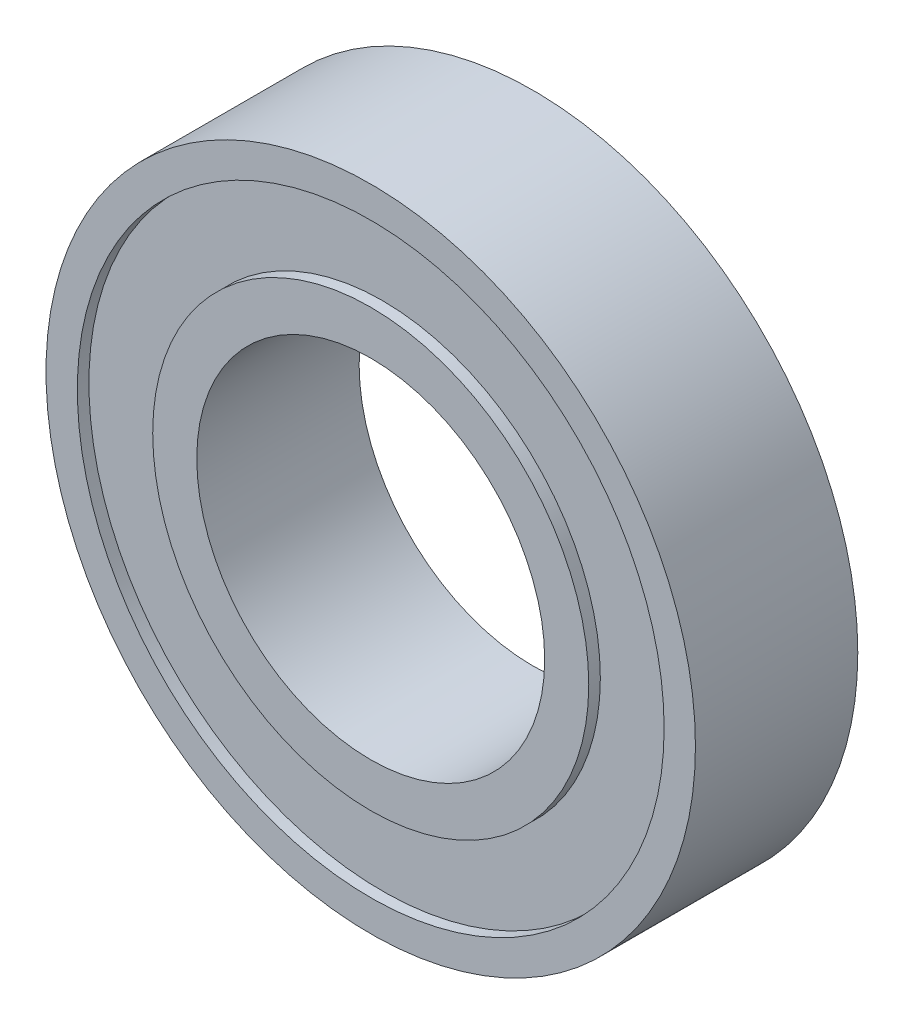
SolidWorks part; units mm, degrees
ref_plane "前基準面" through (0, 0, 0) normal (0, 0, 1) x (1, 0, 0)
ref_plane "上基準面" through (0, 0, 0) normal (0, 1, 0) x (1, 0, 0)
ref_plane "右基準面" through (0, 0, 0) normal (1, 0, 0) x (0, 0, -1)
sketch "草圖1" plane through (0, 0, 0) normal (0, 0, 1) x (1, 0, 0)
  circle A0 centre (0, 0) radius 14
  dimension "D1" = 28
extrude "填料-伸長1" add sketch "草圖1" along normal blind 7
sketch "草圖2" plane through (0, 0, 7) normal (0, 0, 1) x (1, 0, 0)
  circle A0 centre (0, 0) radius 7.5
  dimension "D1" = 15
extrude "除料-伸長1" cut sketch "草圖2" against normal through all
sketch "草圖3" plane through (0, 0, 7) normal (0, 0, 1) x (1, 0, 0)
  circle A0 centre (0, 0) radius 9.4
  circle A1 centre (0, 0) radius 12.65
  dimension "D1" = 18.8
  dimension "D2" = 25.3
extrude "除料-伸長2" cut sketch "草圖3" against normal blind 0.5
sketch "草圖4" plane through (0, 0, 0) normal (0, 0, -1) x (-1, 0, 0)
  circle A0 centre (0, 0) radius 9.4
  circle A1 centre (0, 0) radius 12.65
  dimension "D1" = 18.8
  dimension "D2" = 25.3
extrude "除料-伸長3" cut sketch "草圖4" against normal blind 0.5
